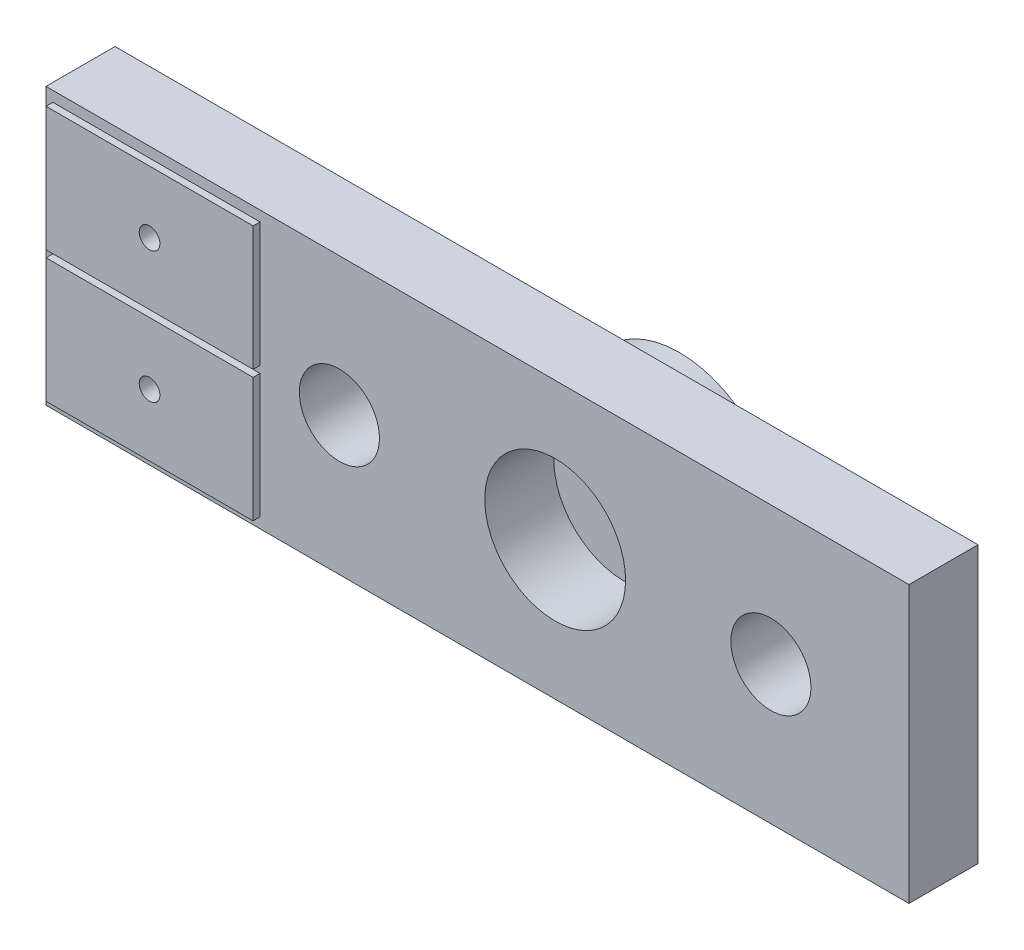
SolidWorks part; units mm, degrees
other "Markup1"
sketch "Sketch3" plane through (-16.256, 5.08, 2.54) normal (-0.0786, 0.0881, 0.993) x (0.9964, 0.0379, 0.0755)
material "S-Glass Fiber"
ref_plane "Front Plane" through (0, 0, 0) normal (0, 0, 1) x (1, 0, 0)
ref_plane "Top Plane" through (0, 0, 0) normal (0, 1, 0) x (1, 0, 0)
ref_plane "Right Plane" through (0, 0, 0) normal (1, 0, 0) x (0, 0, -1)
sketch "Sketch2" plane through (0, 0, 0) normal (0, 0, 1) x (1, 0, 0)
  line L0 (-16.256, 0) -> (15.494, 0) construction
  line L1 (-16.256, 5.08) -> (15.494, 5.08)
  line L2 (-16.256, 5.08) -> (-16.256, -5.08)
  line L3 (-16.256, -5.08) -> (15.494, -5.08)
  line L4 (15.494, 5.08) -> (15.494, -5.08)
  circle A0 centre (-5.461, 0) radius 1.4732
  circle A2 centre (10.414, 0) radius 1.4732
  point P0 (0, 0)
  dimension "D3" = 2.9464
  dimension "D1" = 31.75
  dimension "D2" = 10.16
  dimension "D4" = 15.875
  dimension "D5" = 5.08
extrude "Boss-Extrude1" add sketch "Sketch2" along normal blind 2.54
hole_wizard "#6 (0.204) Diameter Hole1" positions "3DSketch1" profile "Sketch4" hole size "#6" standard "ANSI Inch" end condition through all
sketch3d "3DSketch1"
  line L0 (-16.256, -5.08, 2.54) -> (15.494, -5.08, 2.54) construction
  line L1 (15.494, -5.08, 2.54) -> (15.494, 5.08, 2.54) construction
  point P0 (2.4765, 0, 2.54)
  dimension "D2" = 13.0175
  dimension "D1" = 5.08
sketch "Sketch4" plane through (2.4765, 0, 2.54) normal (1, 0, 0) x (0, -1, 0)
  line L0 (0, 0) -> (0, 2.54)
  line L1 (0, 2.54) -> (2.5908, 2.54)
  line L2 (2.5908, 2.54) -> (2.5908, 0)
  line L5 (2.5908, 0) -> (0, 0)
  line L11 (0, -6.35) -> (0, 107.95) construction
  dimension "Thru Hole Dia." = 5.1816
  dimension "Thru Hole Depth" = 2.54
sketch "Sketch5" plane through (0, 0, 2.54) normal (0, 0, 1) x (1, 0, 0)
  line L0 (-16.256, 0) -> (-7.2764, 0) construction
  line L1 (-16.002, 4.699) -> (-8.382, 4.699)
  line L2 (-16.002, 4.699) -> (-16.002, 0.127)
  line L3 (-16.002, 0.127) -> (-8.382, 0.127)
  line L4 (-8.382, 4.699) -> (-8.382, 0.127)
  line L5 (-16.256, 5.08) -> (-16.256, -5.08) construction
  line L6 (15.494, 5.08) -> (-16.256, 5.08) construction
  line L7 (-8.382, -4.699) -> (-8.382, -0.127)
  line L8 (-16.002, -0.127) -> (-8.382, -0.127)
  line L9 (-16.002, -4.699) -> (-16.002, -0.127)
  line L10 (-16.002, -4.699) -> (-8.382, -4.699)
  dimension "D1" = 4.572
  dimension "D2" = 7.62
  dimension "D3" = 0.381
  dimension "D4" = 0.254
extrude "Boss-Extrude2" add sketch "Sketch5" along normal blind 0.254
sketch "Sketch6" plane through (0, 0, 2.794) normal (0, 0, 1) x (1, 0, 0)
  line L0 (-12.192, 4.699) -> (-12.192, 0.127) construction
  line L1 (-8.382, 4.699) -> (-16.002, 4.699) construction
  line L2 (-16.002, 0.127) -> (-8.382, 0.127) construction
  line L3 (-16.256, 0) -> (-7.1826, 0) construction
  line L4 (-16.256, 5.08) -> (-16.256, -5.08) construction
  circle A0 centre (-12.192, 2.413) radius 0.381
  circle A1 centre (-12.192, -2.413) radius 0.381
  dimension "D1" = 0.762
extrude "Cut-Extrude1" cut sketch "Sketch6" against normal through all
sketch "Sketch7" plane through (0, 0, 0) normal (0, 0, -1) x (-1, 0, 0)
  line L0 (0, 0) -> (-15.494, 0) construction
  line L1 (-15.494, -5.08) -> (-15.494, 5.08) construction
  circle A0 centre (-2.4765, 0) radius 3.683
  dimension "D1" = 7.366
extrude "Boss-Extrude3" add sketch "Sketch7" along normal blind 2.032
equation "\"D2@3DSketch1\"=0.625/2+0.2"
